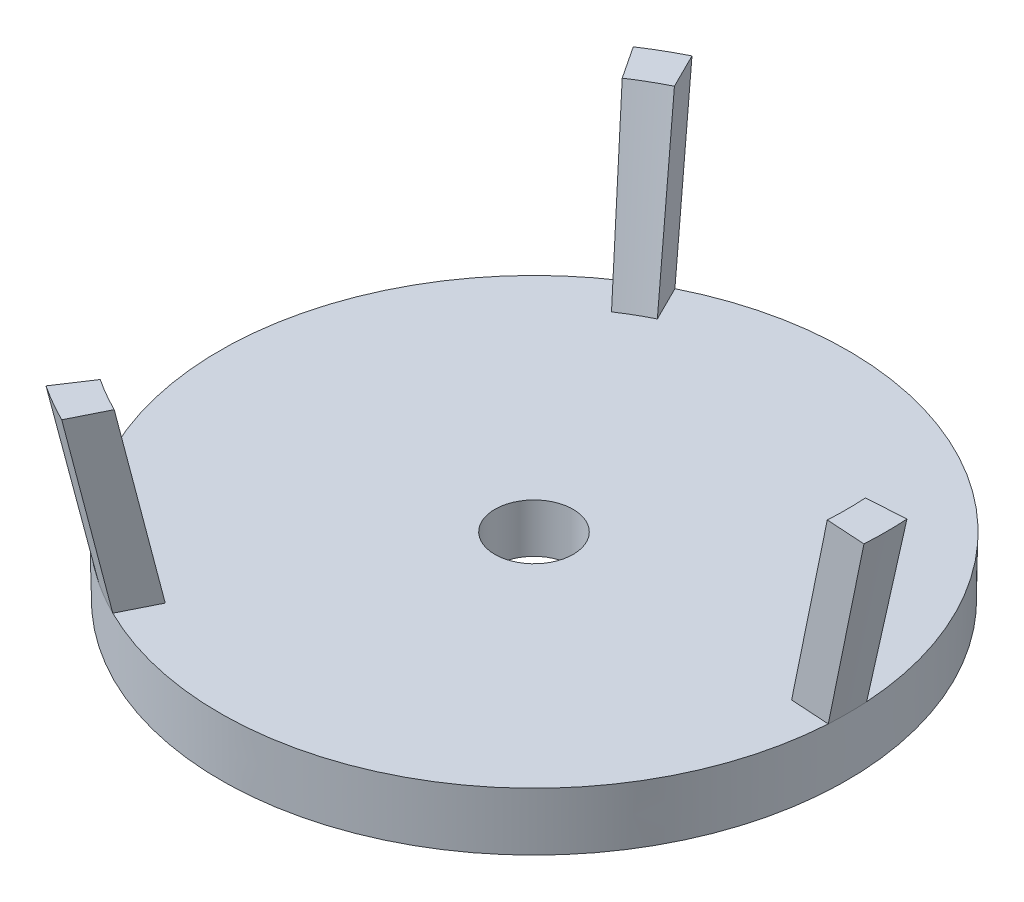
SolidWorks part; units mm, degrees
ref_plane "Front Plane" through (0, 0, 0) normal (0, 0, 1) x (1, 0, 0)
ref_plane "Top Plane" through (0, 0, 0) normal (0, 1, 0) x (1, 0, 0)
ref_plane "Right Plane" through (0, 0, 0) normal (1, 0, 0) x (0, 0, -1)
sketch "Sketch1" plane through (0, 0, 0) normal (0, 0, 1) x (1, 0, 0)
  line L0 (0, 0) -> (0, 16.1217) construction
  line L1 (14, 0) -> (14.0543, 3)
  line L2 (14.0543, 3) -> (16.0543, 3)
  line L3 (16.0543, 3) -> (16, 0)
  line L4 (16, 0) -> (14, 0)
  line L5 (16, 0) -> (16.315, 17.4) construction
revolve "Revolve1" add sketch "Sketch1" angle 360 about L0
ref_plane "Plane2" through (0, 0.5, 0) normal (0, 1, 0) x (1, 0, 0)
sketch "Sketch2" plane through (0, 0, 0) normal (0, 0, 1) x (1, 0, 0)
  line L0 (14.0543, 3) -> (16, 12)
  line L1 (16, 12) -> (18, 12)
  line L2 (18, 12) -> (16.0543, 3)
  line L3 (16.0543, 3) -> (14.0543, 3)
  line L8 (0, 0) -> (0, 2.75) construction
  line L9 (14, 0) -> (14.0543, 3) construction
  dimension "D1" = 12
  dimension "D2" = 36
revolve "Revolve2" add sketch "Sketch2" angle 7 mid plane about L8
pattern_circular "CirPattern1" count 3 over 360 about axis through (0, 0, 0) along (0, 1, 0) of "Revolve2"
sketch "Sketch3" plane through (0, 0.5, 0) normal (0, 1, 0) x (1, 0, 0)
  line L0 (0, 0) -> (13.2009, 0) construction
  arc A1 (11.6744, 0) -> (5.1095, 2.95) centre (6.0259, -3.7904) ccw
  arc A2 (11.6744, 0) -> (5.1095, -2.95) centre (6.0259, 3.7904) cw
  arc A3 (5.8372, -10.1103) -> (0, -5.9) centre (6.2955, -3.3234) cw
  arc A4 (5.8372, -10.1103) -> (5.1095, -2.95) centre (-0.2696, -7.1137) ccw
  arc A5 (-5.8372, -10.1103) -> (-5.1095, -2.95) centre (0.2696, -7.1137) cw
  arc A6 (-5.8372, -10.1103) -> (0, -5.9) centre (-6.2955, -3.3234) ccw
  arc A7 (-11.6744, 0) -> (-5.1095, 2.95) centre (-6.0259, -3.7904) cw
  arc A8 (-11.6744, 0) -> (-5.1095, -2.95) centre (-6.0259, 3.7904) ccw
  arc A9 (-5.8372, 10.1103) -> (0, 5.9) centre (-6.2955, 3.3234) cw
  arc A10 (-5.8372, 10.1103) -> (-5.1095, 2.95) centre (0.2696, 7.1137) ccw
  arc A11 (5.8372, 10.1103) -> (5.1095, 2.95) centre (-0.2696, 7.1137) cw
  arc A12 (5.8372, 10.1103) -> (0, 5.9) centre (6.2955, 3.3234) ccw
  point P38 (0, 0)
  dimension "D2" = 2.95
  dimension "D3" = 11.6744
  dimension "D1" = 6
extrude "Boss-Extrude1" add sketch "Sketch3" along normal blind 0.5 draft 45 separate body
sketch "Sketch4" plane through (0, 1, 0) normal (0, 1, 0) x (1, 0, 0)
  circle A1 centre (0, 0) radius 14.13
extrude "Boss-Extrude2" add sketch "Sketch4" along normal blind 2
sketch "Sketch5" plane through (0, 3, 0) normal (0, 1, 0) x (1, 0, 0)
  circle A0 centre (0, 0) radius 2
extrude "Cut-Extrude1" cut sketch "Sketch5" against normal blind 2.5
equation "\"Base Layer Height\"= .25"
equation "\"Layer Thickness\"= .25"
equation "\"D5@Sketch1\"=\"Base Layer Height\"+\"Layer Thickness\"+2.5"
